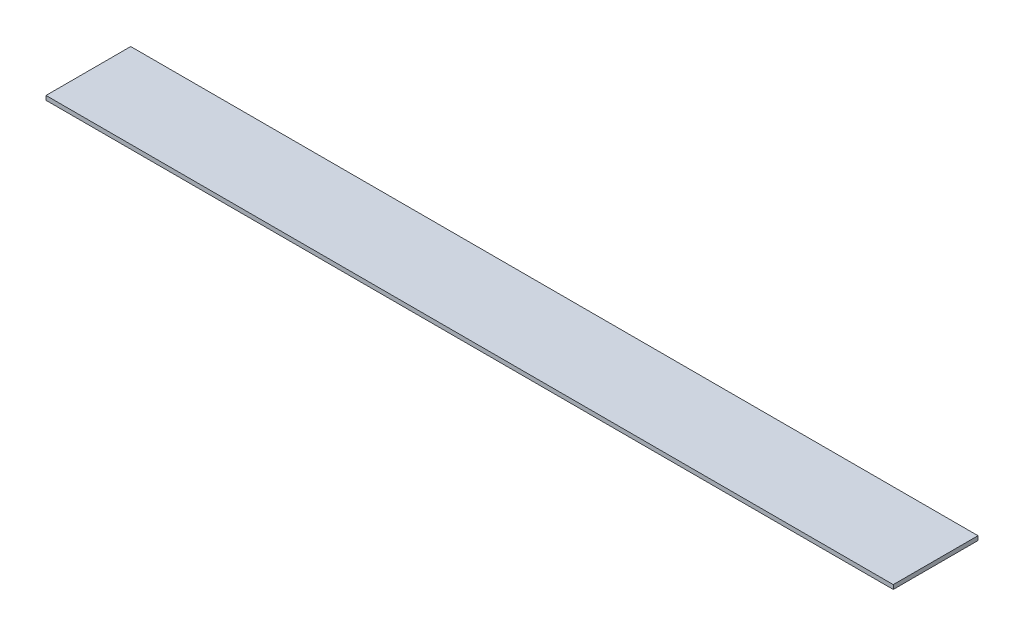
SolidWorks part; units mm, degrees
material "普通碳钢"
ref_plane "前视基准面" through (0, 0, 0) normal (0, 0, 1) x (1, 0, 0)
ref_plane "上视基准面" through (0, 0, 0) normal (0, 1, 0) x (1, 0, 0)
ref_plane "右视基准面" through (0, 0, 0) normal (1, 0, 0) x (0, 0, -1)
sketch "草图1" plane through (0, 0, 0) normal (0, 1, 0) x (1, 0, 0)
  line L1 (-1000, 100) -> (1000, 100)
  line L2 (-1000, 100) -> (-1000, -100)
  line L3 (-1000, -100) -> (1000, -100)
  line L4 (1000, 100) -> (1000, -100)
  line L5 (-1000, 100) -> (1000, -100) construction
  line L6 (-1000, -100) -> (1000, 100) construction
  point P0 (0, 0)
extrude "凸台-拉伸1" add sketch "草图1" along normal blind 10
